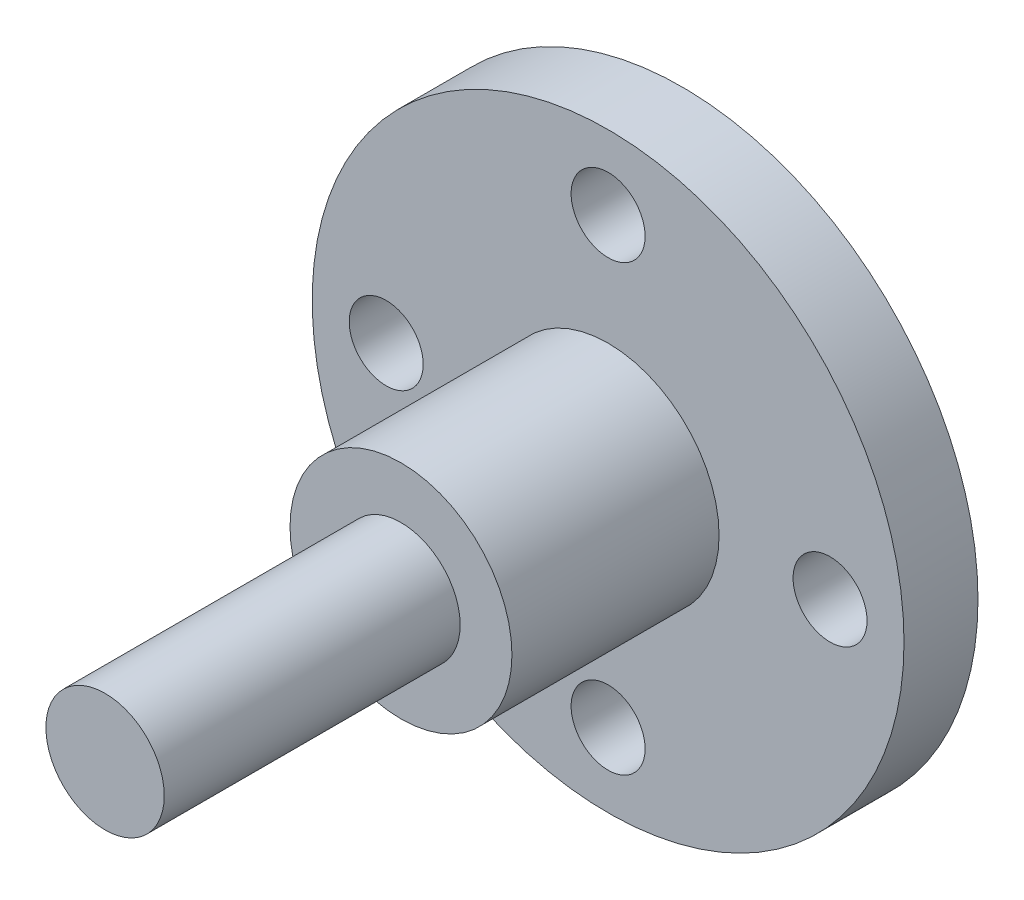
SolidWorks part; units mm, degrees
ref_plane "Front Plane" through (0, 0, 0) normal (0, 0, 1) x (1, 0, 0)
ref_plane "Top Plane" through (0, 0, 0) normal (0, 1, 0) x (1, 0, 0)
ref_plane "Right Plane" through (0, 0, 0) normal (1, 0, 0) x (0, 0, -1)
sketch "Sketch1" plane through (0, 0, 0) normal (0, 0, 1) x (1, 0, 0)
  circle A0 centre (0, 0) radius 20
  dimension "D1" = 40
extrude "Boss-Extrude1" add sketch "Sketch1" along normal blind 5
sketch "Sketch2" plane through (0, 0, 5) normal (0, 0, 1) x (1, 0, 0)
  circle A0 centre (0, 0) radius 7.5
  dimension "D1" = 15
extrude "Boss-Extrude2" add sketch "Sketch2" along normal blind 14
sketch "Sketch3" plane through (0, 0, 19) normal (0, 0, 1) x (1, 0, 0)
  circle A0 centre (0, 0) radius 4
  dimension "D1" = 8
extrude "Boss-Extrude3" add sketch "Sketch3" along normal blind 20
sketch "Sketch4" plane through (0, 0, 5) normal (0, 0, 1) x (1, 0, 0)
  circle A0 centre (0, 0) radius 15 construction
  circle A1 centre (0, 15) radius 2.5
  circle A2 centre (15, 0) radius 2.5
  circle A3 centre (0, -15) radius 2.5
  circle A4 centre (-15, 0) radius 2.5
  point P14 (0, 0)
  dimension "D1" = 30
  dimension "D2" = 5
  dimension "D3" = 4
extrude "Cut-Extrude1" cut sketch "Sketch4" against normal blind 20
